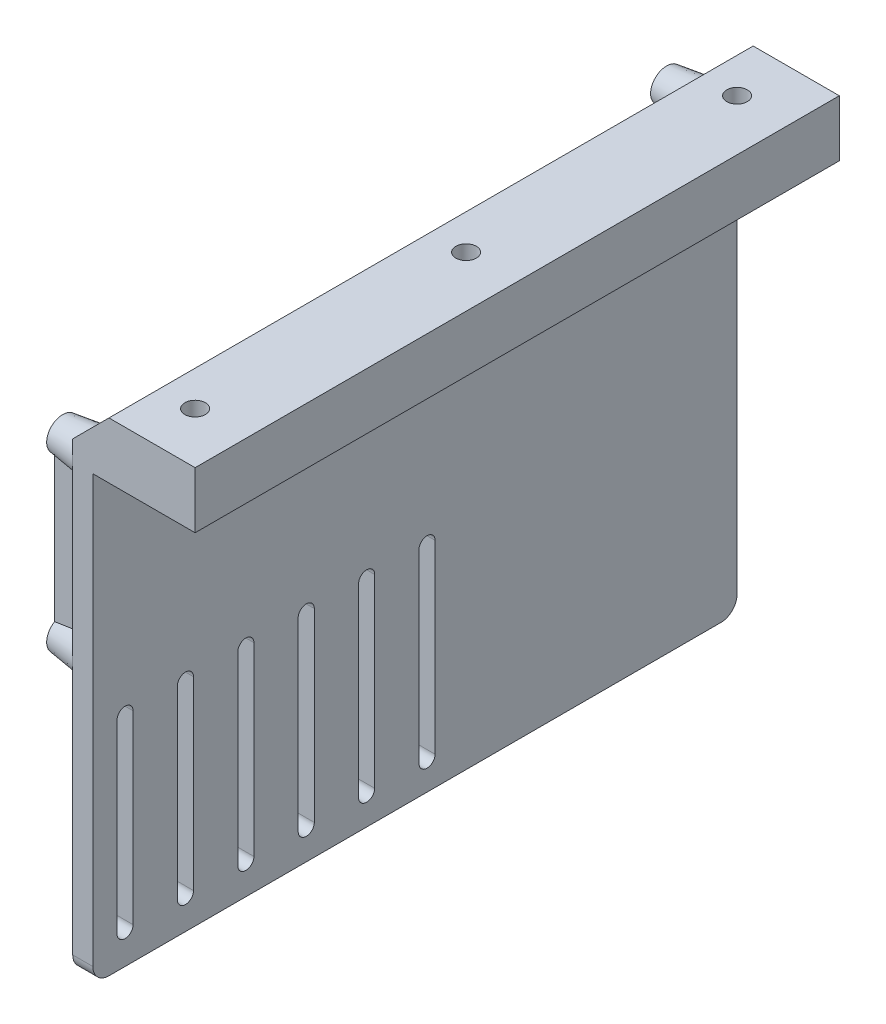
SolidWorks part; units mm, degrees
material "Choose your Material"
ref_plane "Front Plane" through (0, 0, 0) normal (0, 0, 1) x (1, 0, 0)
ref_plane "Top Plane" through (0, 0, 0) normal (0, 1, 0) x (1, 0, 0)
ref_plane "Right Plane" through (0, 0, 0) normal (1, 0, 0) x (0, 0, -1)
sketch "Sketch1" plane through (0, 0, 0) normal (0, 0, 1) x (1, 0, 0)
  line L0 (0, 5) -> (-30.4, 5)
  line L1 (-30.4, 5) -> (-30.4, -110)
  line L2 (-30.4, -110) -> (-25.4, -110)
  line L3 (-25.4, -110) -> (-25.4, 0)
  line L4 (-25.4, 0) -> (0, 0)
  line L5 (0, 0) -> (0, 5)
  point P2 (0, 0)
  dimension "D1" = 5
  dimension "D2" = 25.4
  dimension "D3" = 110
extrude "Boss-Extrude1" add sketch "Sketch1" along normal mid plane 160
sketch "Sketch2" plane through (-30.4, 0, 0) normal (-1, 0, 0) x (0, 0, 1)
  line L0 (80, 5) -> (-80, 5) construction
  line L1 (-75, 0) -> (75, 0) construction
  line L2 (-75, 0) -> (-75, -43) construction
  line L3 (-75, -43) -> (75, -43) construction
  line L4 (75, 0) -> (75, -43) construction
  line L5 (-76, -57) -> (-18, -57) construction
  line L6 (-76, -57) -> (-76, -106) construction
  line L7 (-76, -106) -> (-18, -106) construction
  line L8 (-18, -57) -> (-18, -106) construction
  line L11 (80, -110) -> (-80, -110) construction
  line L12 (-80, 5) -> (-80, -110) construction
  circle A0 centre (75, -43) radius 5
  circle A1 centre (75, 0) radius 5
  circle A2 centre (-75, 0) radius 5
  circle A3 centre (-75, -43) radius 5
  circle A4 centre (-76, -57) radius 4
  circle A5 centre (-76, -106) radius 4
  circle A6 centre (-18, -106) radius 4
  circle A7 centre (-18, -57) radius 4
  dimension "D5" = 10
  dimension "D6" = 8
  dimension "D1" = 150
  dimension "D2" = 43
  dimension "D3" = 58
  dimension "D4" = 49
extrude "Boss-Extrude2" add sketch "Sketch2" along normal blind 7.5 draft 7.8
sketch "Sketch3" plane through (-30.4, 0, 0) normal (-1, 0, 0) x (0, 0, 1)
  line L0 (72, -56) -> (72, -102) construction
  line L1 (74, -56) -> (74, -102)
  line L2 (70, -56) -> (70, -102)
  line L3 (80, -43) -> (80, -110) construction
  line L6 (80, -110) -> (-18, -110) construction
  line L7 (55, -56.1673) -> (55, -102.1673)
  line L8 (59, -56.1673) -> (59, -102.1673)
  line L9 (57, -56.1673) -> (57, -102.1673) construction
  line L10 (40, -56.3346) -> (40, -102.3346)
  line L11 (44, -56.3346) -> (44, -102.3346)
  line L12 (42, -56.3346) -> (42, -102.3346) construction
  line L13 (25, -56.5019) -> (25, -102.5019)
  line L14 (29, -56.5019) -> (29, -102.5019)
  line L15 (27, -56.5019) -> (27, -102.5019) construction
  line L16 (10, -56.6693) -> (10, -102.6693)
  line L17 (14, -56.6693) -> (14, -102.6693)
  line L18 (12, -56.6693) -> (12, -102.6693) construction
  line L19 (-5, -56.8366) -> (-5, -102.8366)
  line L20 (-1, -56.8366) -> (-1, -102.8366)
  line L21 (-3, -56.8366) -> (-3, -102.8366) construction
  arc A0 (74, -56) -> (70, -56) centre (72, -56) ccw
  arc A1 (70, -102) -> (74, -102) centre (72, -102) ccw
  circle A3 centre (75, -43) radius 5 construction
  arc A4 (59, -56.1673) -> (55, -56.1673) centre (57, -56.1673) ccw
  arc A5 (55, -102.1673) -> (59, -102.1673) centre (57, -102.1673) ccw
  arc A6 (44, -56.3346) -> (40, -56.3346) centre (42, -56.3346) ccw
  arc A7 (40, -102.3346) -> (44, -102.3346) centre (42, -102.3346) ccw
  arc A8 (29, -56.5019) -> (25, -56.5019) centre (27, -56.5019) ccw
  arc A9 (25, -102.5019) -> (29, -102.5019) centre (27, -102.5019) ccw
  arc A10 (14, -56.6693) -> (10, -56.6693) centre (12, -56.6693) ccw
  arc A11 (10, -102.6693) -> (14, -102.6693) centre (12, -102.6693) ccw
  arc A12 (-1, -56.8366) -> (-5, -56.8366) centre (-3, -56.8366) ccw
  arc A13 (-5, -102.8366) -> (-1, -102.8366) centre (-3, -102.8366) ccw
  point P2 (72, -79)
  point P16 (57, -79.1673)
  point P23 (42, -79.3346)
  point P30 (27, -79.5019)
  point P37 (12, -79.6693)
  point P44 (-3, -79.8366)
  dimension "D3" = 6
  dimension "D4" = 6
  dimension "D1" = 4
  dimension "D2" = 6
  dimension "D6" = 15
  dimension "D5" = 6
extrude "Cut-Extrude1" cut sketch "Sketch3" against normal through all
sketch "Sketch4" plane through (-30.4, 0, 0) normal (-1, 0, 0) x (0, 0, 1)
  line L0 (80, -110) -> (-18, -110) construction
  line L1 (80, -43) -> (80, -110) construction
  line L2 (80, -106) -> (80, -110) construction
  line L3 (80, -110) -> (76, -110) construction
  line L4 (-80, 0) -> (-80, 5)
  line L5 (-80, 5) -> (-75, 5)
  line L6 (75, 5) -> (80, 5)
  line L7 (80, 5) -> (80, 0)
  line L8 (-80, -106) -> (-80, -110)
  line L9 (-80, -110) -> (-76, -110)
  arc A0 (-80, -106) -> (-76, -110) centre (-76, -106) ccw construction
  arc A1 (-75, 5) -> (-80, 0) centre (-75, 0) ccw construction
  arc A2 (80, 0) -> (75, 5) centre (75, 0) ccw construction
  arc A3 (-80, -106) -> (-76, -110) centre (-76, -106) ccw
  arc A4 (-75, 5) -> (-80, 0) centre (-75, 0) ccw
  arc A5 (80, 0) -> (75, 5) centre (75, 0) ccw
  arc A6 (76, -110) -> (80, -106) centre (76, -106) ccw
  line M30 (-18, -110) -> (80, -110)
  line M31 (80, -110) -> (80, -43)
extrude "Cut-Extrude2" cut sketch "Sketch4" against normal through all contours A6 M30 M31 | A3 L8 L9 | L4 L5 A4
sketch "Sketch6" plane through (-37.9, 0, 0) normal (-1, 0, 0) x (0, 0, 1)
  line L0 (-75, -43) -> (-75, 0)
  line L1 (75, -43) -> (75, 0)
  line L2 (-76, -106) -> (-76, -57)
  line L3 (-76, -57) -> (-75, -43)
  line L4 (-18, -106) -> (-18, -57)
extrude "Extrude-Thin1" add sketch "Sketch6" against normal up to surface (7.5 mm away) thin up to face at (-30.4, -53, -18) thin type mid plane wall 4
hole_wizard "Tap Drill for M2.5x0.45 Tap1" positions "Sketch7" profile "Sketch8" hole size "M2.5x0.45" standard "ANSI Metric"
sketch "Sketch7" plane through (-37.9, 0, 0) normal (-1, 0, 0) x (0, 0, 1)
  point P0 (-76, -57)
  point P3 (-76, -106)
  point P6 (-18, -106)
  point P9 (-18, -57)
sketch "Sketch8" plane through (-37.9, -57, -76) normal (0, 1, 0) x (0, 0, 1)
  line L0 (0, 0) -> (0, 10.6159)
  line L1 (0, 10.6159) -> (1.025, 10)
  line L2 (1.025, 10) -> (1.025, 0)
  line L5 (1.025, 0) -> (0, 0)
  line L10 (0, 10.6159) -> (-1.025, 10) construction
  line L11 (0, -6.35) -> (0, 107.95) construction
  dimension "Hole Dia." = 2.05
  dimension "Hole Depth" = 10
  dimension "Drill Angle" = 118
hole_wizard "Tap Drill for M3x0.5 Tap1" positions "3DSketch1" profile "Sketch9" hole size "M3x0.5" standard "ANSI Metric"
sketch3d "3DSketch1"
  line L0 (-30.4, 0, -75) -> (-37.9, 0, -75) construction
  line L1 (-30.4, -43, -75) -> (-37.9, -43, -75) construction
  line L2 (-30.4, -43, 75) -> (-37.9, -43, 75) construction
  line L3 (-30.4, 0, 75) -> (-37.9, 0, 75) construction
  point P0 (-37.9, 0, -75)
  point P4 (-37.9, -43, -75)
  point P8 (-37.9, -43, 75)
  point P12 (-37.9, 0, 75)
sketch "Sketch9" plane through (-37.9, 0, -75) normal (0, 1, 0) x (0, 0, 1)
  line L0 (0, 0) -> (0, 10.7511)
  line L1 (0, 10.7511) -> (1.25, 10)
  line L2 (1.25, 10) -> (1.25, 0)
  line L5 (1.25, 0) -> (0, 0)
  line L10 (0, 10.7511) -> (-1.25, 10) construction
  line L11 (0, -6.35) -> (0, 107.95) construction
  dimension "Hole Dia." = 2.5
  dimension "Hole Depth" = 10
  dimension "Drill Angle" = 118
sketch "Sketch11" plane through (0, 0, 80) normal (0, 0, 1) x (1, 0, 0)
  line L0 (-30.4, 5) -> (-21.4, 14)
  line L1 (-21.4, 14) -> (0, 14)
  line L2 (0, 14) -> (0, 5)
  line L3 (0, 5) -> (-30.4, 5)
  line L4 (-25.4, 0) -> (0, 0) construction
  dimension "D1" = 45
  dimension "D2" = 14
extrude "Boss-Extrude4" add sketch "Sketch11" against normal up to surface (160 mm away) up to face at (-22.5333, -33.5556, -80)
sketch "Sketch12" plane through (0, 0, 0) normal (0, -1, 0) x (1, 0, 0)
  line L0 (-12.7, 80) -> (-12.7, 67.3) construction
  line L1 (-25.4, 80) -> (0, 80) construction
  line L2 (-12.7, 67.3) -> (-12.7, -67.3) construction
  line L3 (-12.7, -67.3) -> (-12.7, -80) construction
  line L4 (-25.4, -80) -> (0, -80) construction
  line L5 (-12.7, 67.3) -> (0, 67.3) construction
  line L6 (0, 80) -> (0, -80) construction
  circle A0 centre (-12.7, 67.3) radius 3 construction
  circle A1 centre (-12.7, -67.3) radius 3 construction
  circle A2 centre (-12.7, 0) radius 3 construction
  dimension "D1" = 6
hole_wizard "#10 Clearance Hole1" positions "Sketch13" profile "Sketch14" hole size "#10" standard "ANSI Inch" end condition through all
sketch "Sketch13" plane through (0, 0, 0) normal (0, -1, 0) x (-1, 0, 0)
  point P0 (12.7, 0)
  point P3 (12.7, 67.3)
  point P6 (12.7, -67.3)
sketch "Sketch14" plane through (-12.7, 0, 0) normal (1, 0, 0) x (0, 0, -1)
  line L0 (0, 0) -> (0, 14)
  line L1 (0, 14) -> (2.5527, 14)
  line L2 (2.5527, 14) -> (2.5527, 0)
  line L5 (2.5527, 0) -> (0, 0)
  line L11 (0, -6.35) -> (0, 107.95) construction
  dimension "Thru Hole Dia." = 5.1054
  dimension "Thru Hole Depth" = 14
